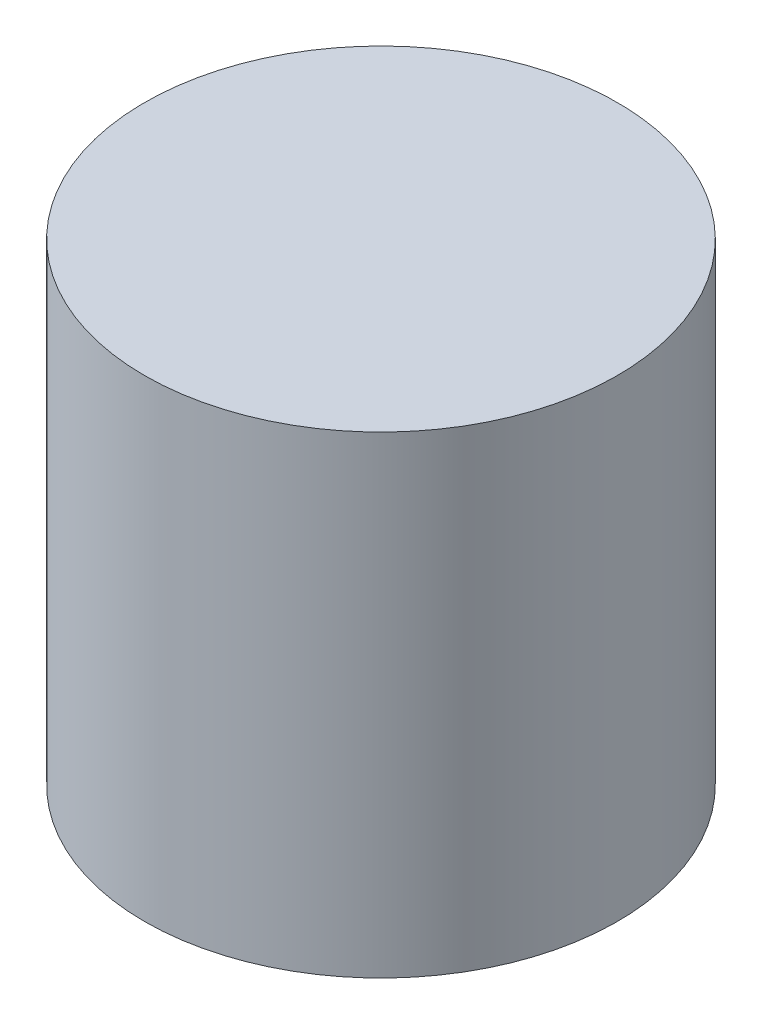
SolidWorks part; units mm, degrees
ref_plane "Front Plane" through (0, 0, 0) normal (0, 0, 1) x (1, 0, 0)
ref_plane "Top Plane" through (0, 0, 0) normal (0, 1, 0) x (1, 0, 0)
ref_plane "Right Plane" through (0, 0, 0) normal (1, 0, 0) x (0, 0, -1)
sketch "Sketch1" plane through (0, 0, 0) normal (0, 1, 0) x (1, 0, 0)
  circle A0 centre (0, 0) radius 1
  dimension "D1" = 2
extrude "Boss-Extrude1" add sketch "Sketch1" along normal blind 2
